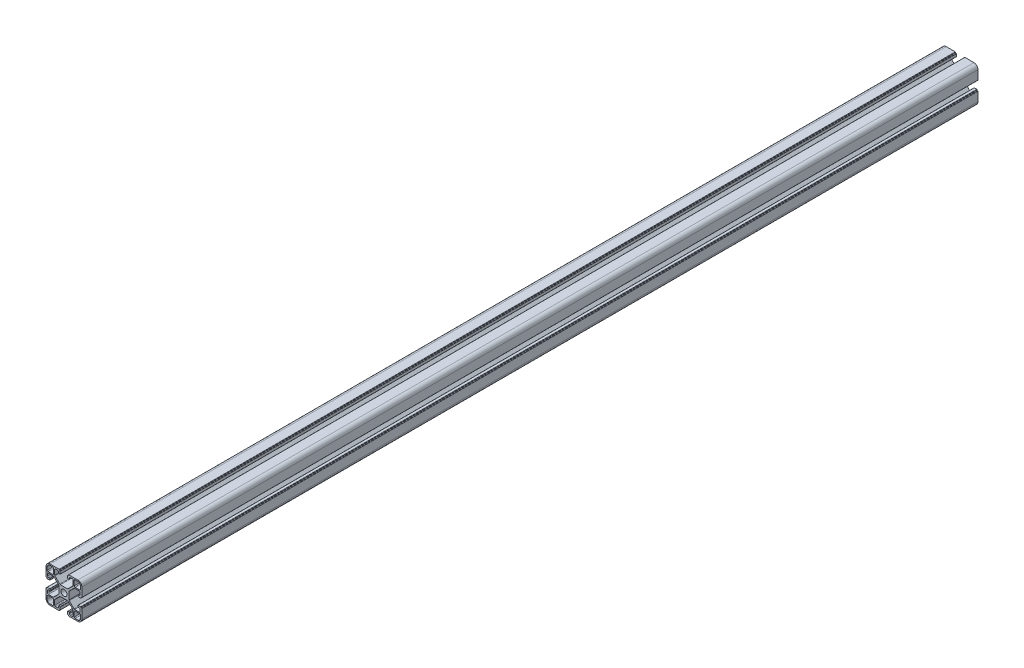
SolidWorks part; units mm, degrees
material "6063 T5"
ref_plane "Спереди" through (0, 0, 0) normal (0, 0, 1) x (1, 0, 0)
ref_plane "Сверху" through (0, 0, 0) normal (0, 1, 0) x (1, 0, 0)
ref_plane "Справа" through (0, 0, 0) normal (1, 0, 0) x (0, 0, -1)
sketch "Эскиз1" plane through (0, 0, 0) normal (0, 0, 1) x (1, 0, 0)
  line L0 (-19.98, 20.5457) -> (20.02, 20.5457) construction
  line L1 (-20, 10.25) -> (-20, 15.5)
  line L2 (-15.5, 20) -> (-10.25, 20)
  line L3 (10.25, 20) -> (15.5, 20)
  line L4 (-12.5, 11.5) -> (-17.7, 11.5)
  line L5 (-11.5, 12.5) -> (-11.5, 17.7)
  line L6 (-12.5, 18.7) -> (-15.5, 18.7)
  line L7 (-18.7, 12.5) -> (-18.7, 15.5)
  line L8 (20, 15.5) -> (20, 10.25)
  line L9 (11.5, 12.5) -> (11.5, 17.7)
  line L10 (12.5, 11.5) -> (17.7, 11.5)
  line L11 (18.7, 12.5) -> (18.7, 15.5)
  line L12 (12.5, 18.7) -> (15.5, 18.7)
  line L13 (20, -10.25) -> (20, -15.5)
  line L14 (15.5, -20) -> (10.25, -20)
  line L15 (12.5, -11.5) -> (17.7, -11.5)
  line L16 (11.5, -12.5) -> (11.5, -17.7)
  line L17 (12.5, -18.7) -> (15.5, -18.7)
  line L18 (18.7, -12.5) -> (18.7, -15.5)
  line L19 (-10.25, -20) -> (-15.5, -20)
  line L20 (-20, -15.5) -> (-20, -10.25)
  line L21 (-11.5, -12.5) -> (-11.5, -17.7)
  line L22 (-12.5, -11.5) -> (-17.7, -11.5)
  line L23 (-18.7, -12.5) -> (-18.7, -15.5)
  line L24 (-12.5, -18.7) -> (-15.5, -18.7)
  line L25 (0, 0) -> (-11.5, 12.5) construction
  arc A0 (-20, 15.5) -> (-15.5, 20) centre (-15.5, 15.5) cw
  arc A1 (-15.5, 18.7) -> (-18.7, 15.5) centre (-15.5, 15.5) ccw
  arc A2 (-17.7, 11.5) -> (-18.7, 12.5) centre (-17.7, 12.5) cw
  arc A3 (-12.5, 11.5) -> (-11.5, 12.5) centre (-12.5, 12.5) ccw
  arc A4 (-11.5, 17.7) -> (-12.5, 18.7) centre (-12.5, 17.7) ccw
  circle A5 centre (0, 0) radius 3.4
  arc A6 (15.5, 20) -> (20, 15.5) centre (15.5, 15.5) cw
  arc A7 (18.7, 15.5) -> (15.5, 18.7) centre (15.5, 15.5) ccw
  arc A8 (11.5, 17.7) -> (12.5, 18.7) centre (12.5, 17.7) cw
  arc A9 (11.5, 12.5) -> (12.5, 11.5) centre (12.5, 12.5) ccw
  arc A10 (17.7, 11.5) -> (18.7, 12.5) centre (17.7, 12.5) ccw
  arc A11 (20, -15.5) -> (15.5, -20) centre (15.5, -15.5) cw
  arc A12 (15.5, -18.7) -> (18.7, -15.5) centre (15.5, -15.5) ccw
  arc A13 (17.7, -11.5) -> (18.7, -12.5) centre (17.7, -12.5) cw
  arc A14 (12.5, -11.5) -> (11.5, -12.5) centre (12.5, -12.5) ccw
  arc A15 (11.5, -17.7) -> (12.5, -18.7) centre (12.5, -17.7) ccw
  arc A16 (-15.5, -20) -> (-20, -15.5) centre (-15.5, -15.5) cw
  arc A17 (-18.7, -15.5) -> (-15.5, -18.7) centre (-15.5, -15.5) ccw
  arc A18 (-11.5, -17.7) -> (-12.5, -18.7) centre (-12.5, -17.7) cw
  arc A19 (-11.5, -12.5) -> (-12.5, -11.5) centre (-12.5, -12.5) ccw
  arc A20 (-17.7, -11.5) -> (-18.7, -12.5) centre (-17.7, -12.5) ccw
  point P5 (0, 0)
  line B0 (-20, 10.25) -> (-20, 5.4)
  line B1 (-19.7, 5.1) -> (-19.3, 5.1)
  line B2 (-19, 4.8) -> (-19, 4.4)
  line B3 (-18.7, 4.1) -> (-16, 4.1)
  line B4 (-15.7, 4.4) -> (-15.7, 5.8)
  line B5 (-16, 6.1) -> (-17.2, 6.1)
  line B6 (-18.2, 7.1) -> (-18.2, 9.25)
  line B7 (-17.2, 10.25) -> (-11.9642, 10.25)
  line B8 (-11.2571, 9.9571) -> (-5.9929, 4.6929)
  line B9 (-5.7, 3.9858) -> (-5.7, -3.9858)
  line B10 (-5.7, 0) -> (-20, 0) construction
  line B11 (-11.2571, -9.9571) -> (-5.9929, -4.6929)
  line B12 (-17.2, -10.25) -> (-11.9642, -10.25)
  line B13 (-18.2, -7.1) -> (-18.2, -9.25)
  line B14 (-16, -6.1) -> (-17.2, -6.1)
  line B15 (-15.7, -4.4) -> (-15.7, -5.8)
  line B16 (-18.7, -4.1) -> (-16, -4.1)
  line B17 (-19, -4.8) -> (-19, -4.4)
  line B18 (-19.7, -5.1) -> (-19.3, -5.1)
  line B19 (-20, -10.25) -> (-20, -5.4)
  arc B20 (-15.7, 5.8) -> (-16, 6.1) centre (-16, 5.8) ccw
  arc B21 (-16, 4.1) -> (-15.7, 4.4) centre (-16, 4.4) ccw
  arc B22 (-19, 4.4) -> (-18.7, 4.1) centre (-18.7, 4.4) ccw
  arc B23 (-19.3, 5.1) -> (-19, 4.8) centre (-19.3, 4.8) cw
  arc B24 (-20, 5.4) -> (-19.7, 5.1) centre (-19.7, 5.4) ccw
  arc B25 (-5.9929, 4.6929) -> (-5.7, 3.9858) centre (-6.7, 3.9858) cw
  arc B26 (-11.9642, 10.25) -> (-11.2571, 9.9571) centre (-11.9642, 9.25) cw
  arc B27 (-18.2, 9.25) -> (-17.2, 10.25) centre (-17.2, 9.25) cw
  arc B28 (-17.2, 6.1) -> (-18.2, 7.1) centre (-17.2, 7.1) cw
  arc B29 (-17.2, -6.1) -> (-18.2, -7.1) centre (-17.2, -7.1) ccw
  arc B30 (-18.2, -9.25) -> (-17.2, -10.25) centre (-17.2, -9.25) ccw
  arc B31 (-11.9642, -10.25) -> (-11.2571, -9.9571) centre (-11.9642, -9.25) ccw
  arc B32 (-5.9929, -4.6929) -> (-5.7, -3.9858) centre (-6.7, -3.9858) ccw
  arc B33 (-20, -5.4) -> (-19.7, -5.1) centre (-19.7, -5.4) cw
  arc B34 (-19.3, -5.1) -> (-19, -4.8) centre (-19.3, -4.8) ccw
  arc B35 (-19, -4.4) -> (-18.7, -4.1) centre (-18.7, -4.4) cw
  arc B36 (-16, -4.1) -> (-15.7, -4.4) centre (-16, -4.4) cw
  arc B37 (-15.7, -5.8) -> (-16, -6.1) centre (-16, -5.8) cw
  line B38 (10.25, 20) -> (5.4, 20)
  line B39 (5.1, 19.7) -> (5.1, 19.3)
  line B40 (4.8, 19) -> (4.4, 19)
  line B41 (4.1, 18.7) -> (4.1, 16)
  line B42 (4.4, 15.7) -> (5.8, 15.7)
  line B43 (6.1, 16) -> (6.1, 17.2)
  line B44 (7.1, 18.2) -> (9.25, 18.2)
  line B45 (10.25, 17.2) -> (10.25, 11.9642)
  line B46 (9.9571, 11.2571) -> (4.6929, 5.9929)
  line B47 (3.9858, 5.7) -> (-3.9858, 5.7)
  line B48 (0, 5.7) -> (0, 20) construction
  line B49 (-9.9571, 11.2571) -> (-4.6929, 5.9929)
  line B50 (-10.25, 17.2) -> (-10.25, 11.9642)
  line B51 (-7.1, 18.2) -> (-9.25, 18.2)
  line B52 (-6.1, 16) -> (-6.1, 17.2)
  line B53 (-4.4, 15.7) -> (-5.8, 15.7)
  line B54 (-4.1, 18.7) -> (-4.1, 16)
  line B55 (-4.8, 19) -> (-4.4, 19)
  line B56 (-5.1, 19.7) -> (-5.1, 19.3)
  line B57 (-10.25, 20) -> (-5.4, 20)
  arc B58 (5.8, 15.7) -> (6.1, 16) centre (5.8, 16) ccw
  arc B59 (4.1, 16) -> (4.4, 15.7) centre (4.4, 16) ccw
  arc B60 (4.4, 19) -> (4.1, 18.7) centre (4.4, 18.7) ccw
  arc B61 (5.1, 19.3) -> (4.8, 19) centre (4.8, 19.3) cw
  arc B62 (5.4, 20) -> (5.1, 19.7) centre (5.4, 19.7) ccw
  arc B63 (4.6929, 5.9929) -> (3.9858, 5.7) centre (3.9858, 6.7) cw
  arc B64 (10.25, 11.9642) -> (9.9571, 11.2571) centre (9.25, 11.9642) cw
  arc B65 (9.25, 18.2) -> (10.25, 17.2) centre (9.25, 17.2) cw
  arc B66 (6.1, 17.2) -> (7.1, 18.2) centre (7.1, 17.2) cw
  arc B67 (-6.1, 17.2) -> (-7.1, 18.2) centre (-7.1, 17.2) ccw
  arc B68 (-9.25, 18.2) -> (-10.25, 17.2) centre (-9.25, 17.2) ccw
  arc B69 (-10.25, 11.9642) -> (-9.9571, 11.2571) centre (-9.25, 11.9642) ccw
  arc B70 (-4.6929, 5.9929) -> (-3.9858, 5.7) centre (-3.9858, 6.7) ccw
  arc B71 (-5.4, 20) -> (-5.1, 19.7) centre (-5.4, 19.7) cw
  arc B72 (-5.1, 19.3) -> (-4.8, 19) centre (-4.8, 19.3) ccw
  arc B73 (-4.4, 19) -> (-4.1, 18.7) centre (-4.4, 18.7) cw
  arc B74 (-4.1, 16) -> (-4.4, 15.7) centre (-4.4, 16) cw
  arc B75 (-5.8, 15.7) -> (-6.1, 16) centre (-5.8, 16) cw
  line B76 (20, -10.25) -> (20, -5.4)
  line B77 (19.7, -5.1) -> (19.3, -5.1)
  line B78 (19, -4.8) -> (19, -4.4)
  line B79 (18.7, -4.1) -> (16, -4.1)
  line B80 (15.7, -4.4) -> (15.7, -5.8)
  line B81 (16, -6.1) -> (17.2, -6.1)
  line B82 (18.2, -7.1) -> (18.2, -9.25)
  line B83 (17.2, -10.25) -> (11.9642, -10.25)
  line B84 (11.2571, -9.9571) -> (5.9929, -4.6929)
  line B85 (5.7, -3.9858) -> (5.7, 3.9858)
  line B86 (5.7, 0) -> (20, 0) construction
  line B87 (11.2571, 9.9571) -> (5.9929, 4.6929)
  line B88 (17.2, 10.25) -> (11.9642, 10.25)
  line B89 (18.2, 7.1) -> (18.2, 9.25)
  line B90 (16, 6.1) -> (17.2, 6.1)
  line B91 (15.7, 4.4) -> (15.7, 5.8)
  line B92 (18.7, 4.1) -> (16, 4.1)
  line B93 (19, 4.8) -> (19, 4.4)
  line B94 (19.7, 5.1) -> (19.3, 5.1)
  line B95 (20, 10.25) -> (20, 5.4)
  arc B96 (15.7, -5.8) -> (16, -6.1) centre (16, -5.8) ccw
  arc B97 (16, -4.1) -> (15.7, -4.4) centre (16, -4.4) ccw
  arc B98 (19, -4.4) -> (18.7, -4.1) centre (18.7, -4.4) ccw
  arc B99 (19.3, -5.1) -> (19, -4.8) centre (19.3, -4.8) cw
  arc B100 (20, -5.4) -> (19.7, -5.1) centre (19.7, -5.4) ccw
  arc B101 (5.9929, -4.6929) -> (5.7, -3.9858) centre (6.7, -3.9858) cw
  arc B102 (11.9642, -10.25) -> (11.2571, -9.9571) centre (11.9642, -9.25) cw
  arc B103 (18.2, -9.25) -> (17.2, -10.25) centre (17.2, -9.25) cw
  arc B104 (17.2, -6.1) -> (18.2, -7.1) centre (17.2, -7.1) cw
  arc B105 (17.2, 6.1) -> (18.2, 7.1) centre (17.2, 7.1) ccw
  arc B106 (18.2, 9.25) -> (17.2, 10.25) centre (17.2, 9.25) ccw
  arc B107 (11.9642, 10.25) -> (11.2571, 9.9571) centre (11.9642, 9.25) ccw
  arc B108 (5.9929, 4.6929) -> (5.7, 3.9858) centre (6.7, 3.9858) ccw
  arc B109 (20, 5.4) -> (19.7, 5.1) centre (19.7, 5.4) cw
  arc B110 (19.3, 5.1) -> (19, 4.8) centre (19.3, 4.8) ccw
  arc B111 (19, 4.4) -> (18.7, 4.1) centre (18.7, 4.4) cw
  arc B112 (16, 4.1) -> (15.7, 4.4) centre (16, 4.4) cw
  arc B113 (15.7, 5.8) -> (16, 6.1) centre (16, 5.8) cw
  line B114 (-10.25, -20) -> (-5.4, -20)
  line B115 (-5.1, -19.7) -> (-5.1, -19.3)
  line B116 (-4.8, -19) -> (-4.4, -19)
  line B117 (-4.1, -18.7) -> (-4.1, -16)
  line B118 (-4.4, -15.7) -> (-5.8, -15.7)
  line B119 (-6.1, -16) -> (-6.1, -17.2)
  line B120 (-7.1, -18.2) -> (-9.25, -18.2)
  line B121 (-10.25, -17.2) -> (-10.25, -11.9642)
  line B122 (-9.9571, -11.2571) -> (-4.6929, -5.9929)
  line B123 (-3.9858, -5.7) -> (3.9858, -5.7)
  line B124 (0, -5.7) -> (0, -20) construction
  line B125 (9.9571, -11.2571) -> (4.6929, -5.9929)
  line B126 (10.25, -17.2) -> (10.25, -11.9642)
  line B127 (7.1, -18.2) -> (9.25, -18.2)
  line B128 (6.1, -16) -> (6.1, -17.2)
  line B129 (4.4, -15.7) -> (5.8, -15.7)
  line B130 (4.1, -18.7) -> (4.1, -16)
  line B131 (4.8, -19) -> (4.4, -19)
  line B132 (5.1, -19.7) -> (5.1, -19.3)
  line B133 (10.25, -20) -> (5.4, -20)
  arc B134 (-5.8, -15.7) -> (-6.1, -16) centre (-5.8, -16) ccw
  arc B135 (-4.1, -16) -> (-4.4, -15.7) centre (-4.4, -16) ccw
  arc B136 (-4.4, -19) -> (-4.1, -18.7) centre (-4.4, -18.7) ccw
  arc B137 (-5.1, -19.3) -> (-4.8, -19) centre (-4.8, -19.3) cw
  arc B138 (-5.4, -20) -> (-5.1, -19.7) centre (-5.4, -19.7) ccw
  arc B139 (-4.6929, -5.9929) -> (-3.9858, -5.7) centre (-3.9858, -6.7) cw
  arc B140 (-10.25, -11.9642) -> (-9.9571, -11.2571) centre (-9.25, -11.9642) cw
  arc B141 (-9.25, -18.2) -> (-10.25, -17.2) centre (-9.25, -17.2) cw
  arc B142 (-6.1, -17.2) -> (-7.1, -18.2) centre (-7.1, -17.2) cw
  arc B143 (6.1, -17.2) -> (7.1, -18.2) centre (7.1, -17.2) ccw
  arc B144 (9.25, -18.2) -> (10.25, -17.2) centre (9.25, -17.2) ccw
  arc B145 (10.25, -11.9642) -> (9.9571, -11.2571) centre (9.25, -11.9642) ccw
  arc B146 (4.6929, -5.9929) -> (3.9858, -5.7) centre (3.9858, -6.7) ccw
  arc B147 (5.4, -20) -> (5.1, -19.7) centre (5.4, -19.7) cw
  arc B148 (5.1, -19.3) -> (4.8, -19) centre (4.8, -19.3) ccw
  arc B149 (4.4, -19) -> (4.1, -18.7) centre (4.4, -18.7) cw
  arc B150 (4.1, -16) -> (4.4, -15.7) centre (4.4, -16) cw
  arc B151 (5.8, -15.7) -> (6.1, -16) centre (5.8, -16) cw
  dimension "D2" = 4.5
  dimension "D3" = 3.2
  dimension "D5" = 1
  dimension "D6" = 6.8
  dimension "D1" = 20
  dimension "D4" = 7.2
sketch_block_instance "8B(20,5PL)-1"
sketch_block "8B(20,5PL)" parameters "D7"=0.3, "D8"=1, "D1"=14.3, "D2"=4.3, "D3"=8.2, "D4"=20.5, "D5"=10.2, "D6"=135, "D9"=4.85, "D10"=1.2, "D11"=2.15, "D12"=11.8
sketch_block_instance "8B(20,5PL)-3"
sketch_block_instance "8B(20,5PL)-4"
sketch_block_instance "8B(20,5PL)-5"
extrude "Бобышка-Вытянуть1" add sketch "Эскиз1" along normal blind 1000 contours B151 B129 B150 B130 B149 B131 B148 B132 B147 B133 L14 A11 L13 B76 B100 B77 B99 B78 B98 B79 B97 B80 B96 B81 B104 B82 B103 B83 B102 B84 B101 B85 B108 B87 B107 B88 B106 B89 B105 B90 B113 B91 B112 B92 B111 B93 B110 B94 B109 B95 L8
